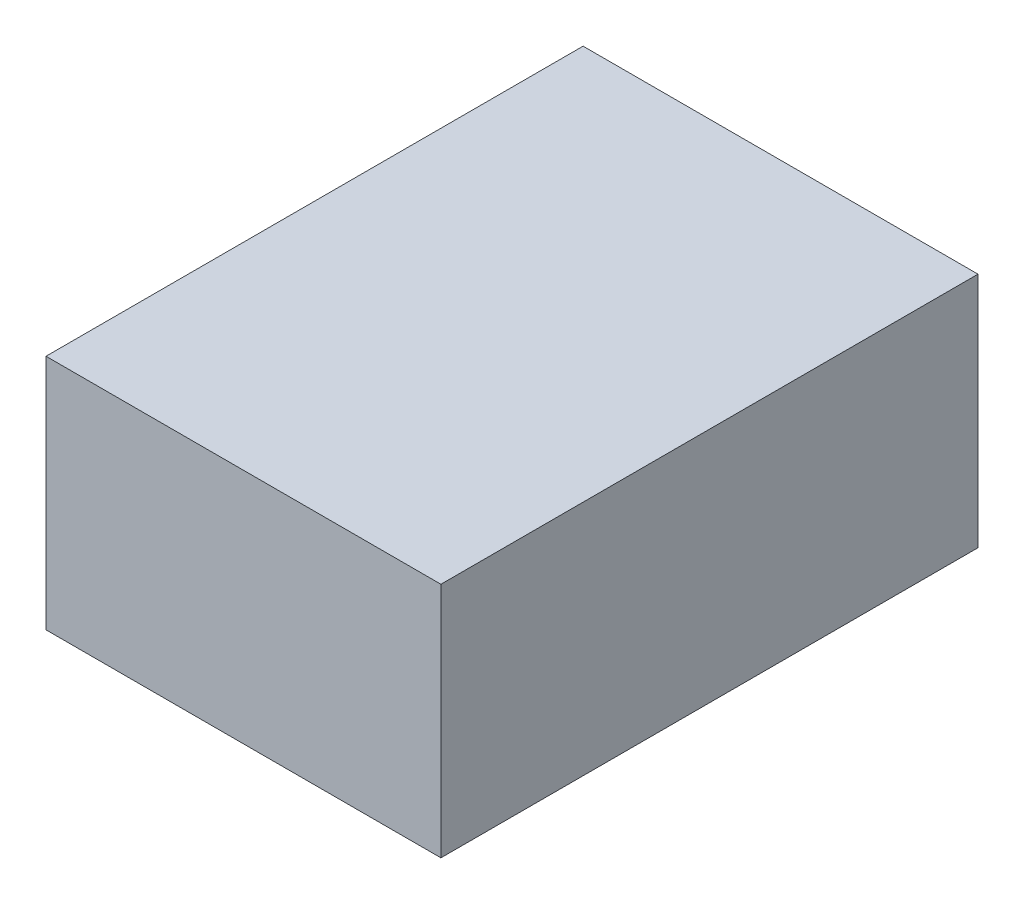
SolidWorks part; units mm, degrees
material "Balsa"
ref_plane "Front Plane" through (0, 0, 0) normal (0, 0, 1) x (1, 0, 0)
ref_plane "Top Plane" through (0, 0, 0) normal (0, 1, 0) x (1, 0, 0)
ref_plane "Right Plane" through (0, 0, 0) normal (1, 0, 0) x (0, 0, -1)
sketch "Sketch1" plane through (0, 0, 0) normal (0, 1, 0) x (1, 0, 0)
  line L1 (0, 0) -> (63.5, 0)
  line L2 (0, 0) -> (0, 86.36)
  line L3 (0, 86.36) -> (63.5, 86.36)
  line L4 (63.5, 0) -> (63.5, 86.36)
  dimension "D1" = 86.36
  dimension "D2" = 63.5
extrude "Boss-Extrude1" add sketch "Sketch1" along normal blind 38.1
